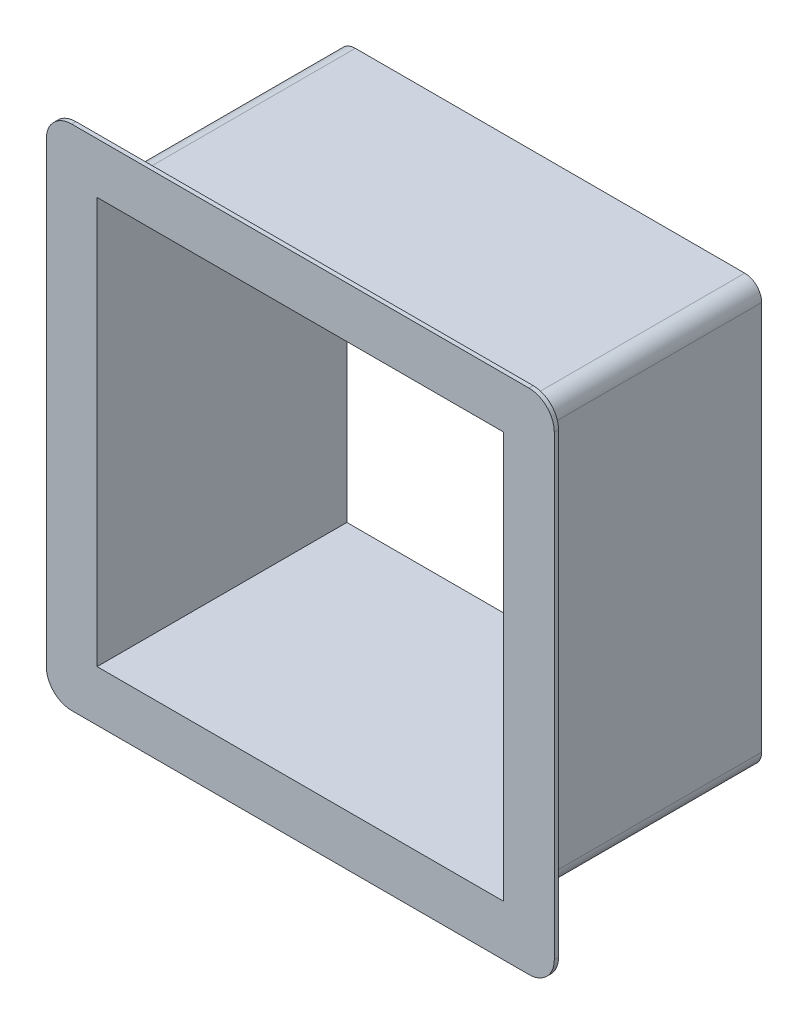
SolidWorks part; units mm, degrees
material "PVC Rigid"
ref_plane "Front Plane" through (0, 0, 0) normal (0, 0, 1) x (1, 0, 0)
ref_plane "Top Plane" through (0, 0, 0) normal (0, 1, 0) x (1, 0, 0)
ref_plane "Right Plane" through (0, 0, 0) normal (1, 0, 0) x (0, 0, -1)
sketch "Sketch1" plane through (0, 0, 0) normal (0, 0, 1) x (1, 0, 0)
  line L1 (-48, -48) -> (48, -48)
  line L2 (-48, -48) -> (-48, 48)
  line L3 (-48, 48) -> (48, 48)
  line L4 (48, -48) -> (48, 48)
  line L5 (-48, -48) -> (48, 48) construction
  line L6 (-48, 48) -> (48, -48) construction
  line L7 (-50, -50) -> (50, -50)
  line L8 (-50, -50) -> (-50, 50)
  line L9 (-50, 50) -> (50, 50)
  line L10 (50, -50) -> (50, 50)
  line L11 (-50, -50) -> (50, 50) construction
  line L12 (-50, 50) -> (50, -50) construction
  point P0 (0, 0)
  point P6 (0, 0)
extrude "Boss-Extrude1" add sketch "Sketch1" against normal blind 59 contours L8 L9 L10 L7 | L2 L3 L4 L1
sketch "Sketch2" plane through (0, 0, 0) normal (0, 0, 1) x (1, 0, 0)
  line L1 (-50, -50) -> (50, -50)
  line L2 (-50, -50) -> (-50, 50)
  line L3 (-50, 50) -> (50, 50)
  line L4 (50, -50) -> (50, 50)
  line L5 (-50, -50) -> (50, 50) construction
  line L6 (-50, 50) -> (50, -50) construction
  line L7 (-60, -60) -> (60, -60)
  line L8 (-60, -60) -> (-60, 60)
  line L9 (-60, 60) -> (60, 60)
  line L10 (60, -60) -> (60, 60)
  line L11 (-60, -60) -> (60, 60) construction
  line L12 (-60, 60) -> (60, -60) construction
  point P0 (0, 0)
  point P7 (0, 0)
extrude "Boss-Extrude4" add sketch "Sketch2" against normal blind 1 contours L4 L3 L2 L1 | L10 L9 L8 L7
ref_plane "Plane1" through (0, 0, -30) normal (0, 0, -1) x (-1, 0, 0)
sketch "Sketch3" plane through (0, 0, -30) normal (0, 0, -1) x (-1, 0, 0)
  line L0 (-48, 0) -> (48, 0) construction
  line L1 (48, -48) -> (48, 48) construction
  point P6 (0, 0)
sketch "Sketch4" plane through (-48, 0, 0) normal (1, 0, 0) x (0, 0, -1)
  line L1 (29, -1) -> (31, -1)
  line L2 (29, -1) -> (29, 1)
  line L3 (29, 1) -> (31, 1)
  line L4 (31, -1) -> (31, 1)
  line L5 (29, -1) -> (31, 1) construction
  line L6 (29, 1) -> (31, -1) construction
  point P0 (30, 0)
sketch "Sketch5" plane through (48, 0, 0) normal (-1, 0, 0) x (0, 0, 1)
  line L1 (-31, -1) -> (-29, -1)
  line L2 (-31, -1) -> (-31, 1)
  line L3 (-31, 1) -> (-29, 1)
  line L4 (-29, -1) -> (-29, 1)
  line L5 (-31, -1) -> (-29, 1) construction
  line L6 (-31, 1) -> (-29, -1) construction
  point P0 (-30, 0)
fillet "Fillet1" radius 4 4 edges at (50, -50, -30) (-50, -50, -30) (-50, 50, -30) (50, 50, -30)
fillet "Fillet2" radius 6 4 edges at (60, -60, -0.5) (-60, -60, -0.5) (-60, 60, -0.5) (60, 60, -0.5)
